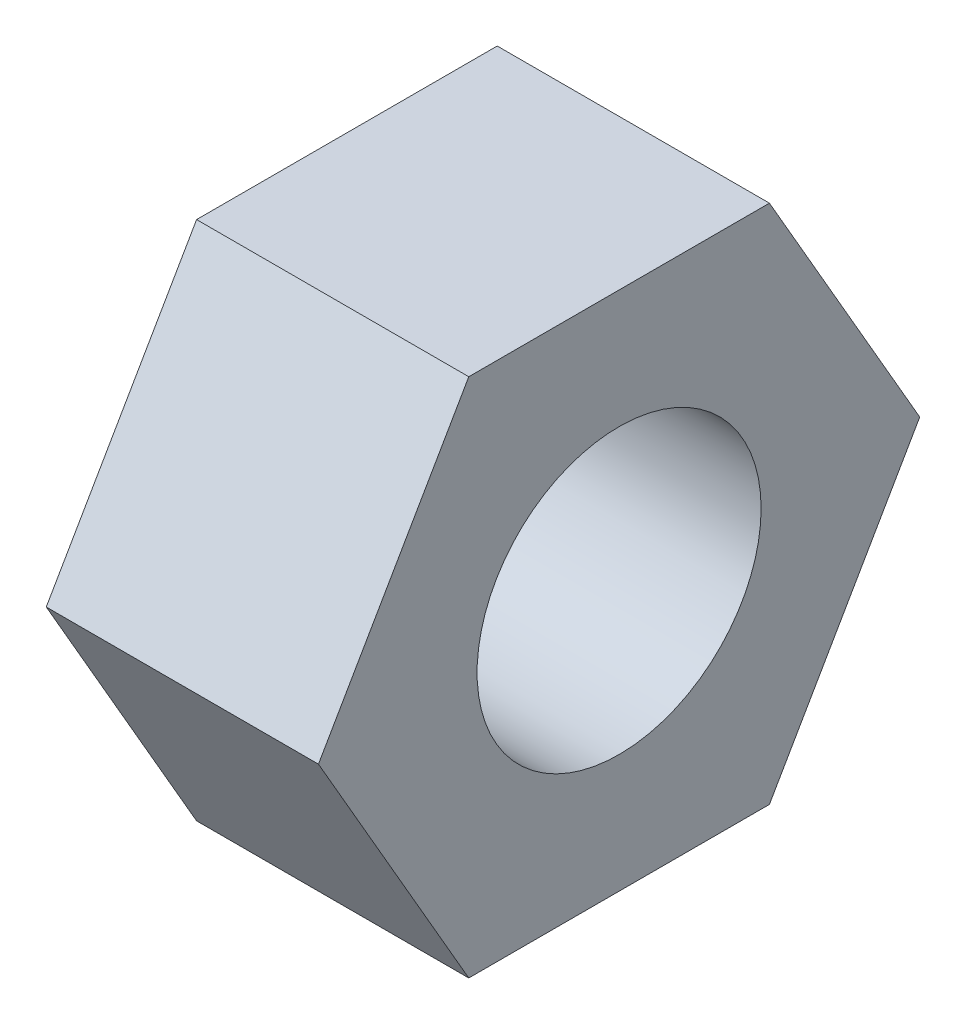
SolidWorks part; units mm, degrees
ref_plane "Front Plane" through (0, 0, 0) normal (0, 0, 1) x (1, 0, 0)
ref_plane "Top Plane" through (0, 0, 0) normal (0, 1, 0) x (1, 0, 0)
ref_plane "Right Plane" through (0, 0, 0) normal (1, 0, 0) x (0, 0, -1)
sketch "Sketch1" plane through (0, 0, 0) normal (1, 0, 0) x (0, 0, -1)
  line L2 (-10.082, 0) -> (-5.041, -8.7313)
  line L3 (-5.041, -8.7313) -> (5.041, -8.7313)
  line L4 (5.041, -8.7313) -> (10.082, 0)
  line L5 (10.082, 0) -> (5.041, 8.7313)
  line L6 (5.041, 8.7313) -> (-5.041, 8.7313)
  line L7 (-5.041, 8.7313) -> (-10.082, 0)
  circle A1 centre (0, 0) radius 4.7625
extrude "Boss-Extrude1" add sketch "Sketch1" along normal blind 9.1281
